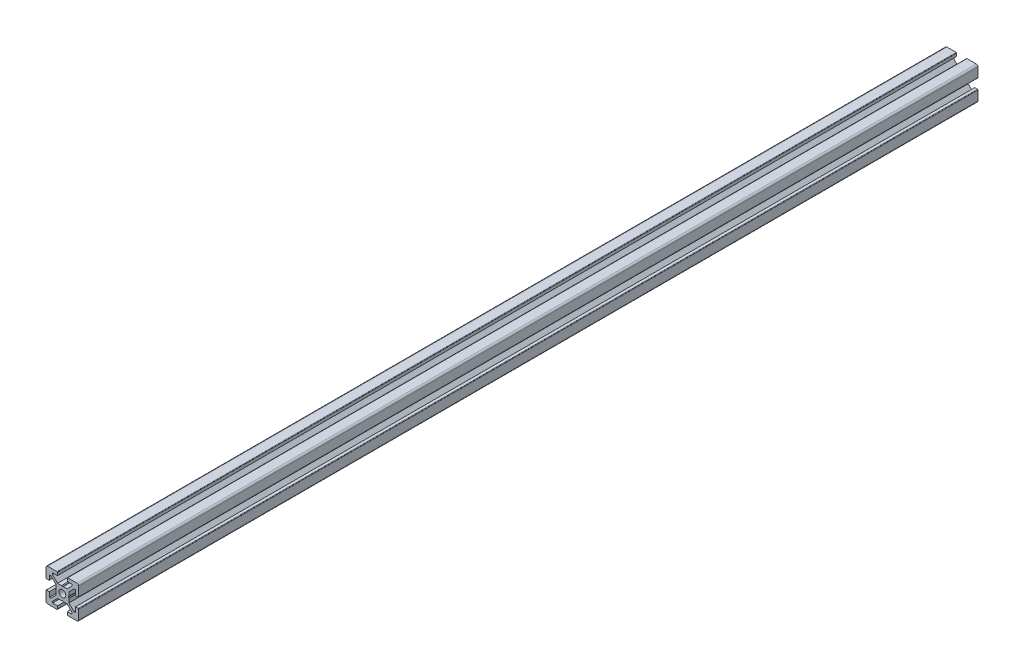
SolidWorks part; units mm, degrees
ref_plane "Front" through (0, 0, 0) normal (0, 0, 1) x (1, 0, 0)
ref_plane "Top" through (0, 0, 0) normal (0, 1, 0) x (1, 0, 0)
ref_plane "Right" through (0, 0, 0) normal (1, 0, 0) x (0, 0, -1)
ref_plane "Plane1" through (0, 0, 0) normal (0, 0, 1) x (1, 0, 0)
sketch "Sketch1" plane through (0, 0, 0) normal (0, 0, 1) x (1, 0, 0)
  line L0 (-10, 9) -> (-10, 3.3)
  line L1 (-9.7, 3) -> (-8, 3)
  line L2 (-8, 3) -> (-8, 6)
  line L3 (-8, 6) -> (-7.0607, 6)
  line L4 (-7.0607, 6) -> (-4, 2.9393)
  line L5 (-4, 2.9393) -> (-4, 0.5196)
  line L6 (-4, 0.5196) -> (-3.7, 0)
  line L7 (-3.7, 0) -> (-4, -0.5196)
  line L8 (-4, -0.5196) -> (-4, -2.9393)
  line L9 (-4, -2.9393) -> (-7.0607, -6)
  line L10 (-7.0607, -6) -> (-8, -6)
  line L11 (-8, -6) -> (-8, -3)
  line L12 (-8, -3) -> (-9.7, -3)
  line L13 (-10, -3.3) -> (-10, -9)
  line L14 (-9, -10) -> (-3.3, -10)
  line L15 (-3, -9.7) -> (-3, -8)
  line L16 (-3, -8) -> (-6, -8)
  line L17 (-6, -8) -> (-6, -7.0607)
  line L18 (-6, -7.0607) -> (-2.9393, -4)
  line L19 (-2.9393, -4) -> (-0.5196, -4)
  line L20 (-0.5196, -4) -> (0, -3.7)
  line L21 (0, -3.7) -> (0.5196, -4)
  line L22 (0.5196, -4) -> (2.9393, -4)
  line L23 (2.9393, -4) -> (6, -7.0607)
  line L24 (6, -7.0607) -> (6, -8)
  line L25 (6, -8) -> (3, -8)
  line L26 (3, -8) -> (3, -9.7)
  line L27 (3.3, -10) -> (9, -10)
  line L28 (10, -9) -> (10, -3.3)
  line L29 (9.7, -3) -> (8, -3)
  line L30 (8, -3) -> (8, -6)
  line L31 (8, -6) -> (7.0606, -6)
  line L32 (7.0606, -6) -> (4, -2.9393)
  line L33 (4, -2.9393) -> (4, -0.5196)
  line L34 (4, -0.5196) -> (3.7, 0)
  line L35 (3.7, 0) -> (4, 0.5196)
  line L36 (4, 0.5196) -> (4, 2.9393)
  line L37 (4, 2.9393) -> (7.0607, 6)
  line L38 (7.0607, 6) -> (8, 6)
  line L39 (8, 6) -> (8, 3)
  line L40 (8, 3) -> (9.7, 3)
  line L41 (10, 3.3) -> (10, 9)
  line L42 (9, 10) -> (3.3, 10)
  line L43 (3, 9.7) -> (3, 8)
  line L44 (3, 8) -> (6, 8)
  line L45 (6, 8) -> (6, 7.0607)
  line L46 (6, 7.0607) -> (2.9393, 4)
  line L47 (2.9393, 4) -> (0.5196, 4)
  line L48 (0.5196, 4) -> (0, 3.7)
  line L49 (0, 3.7) -> (-0.5196, 4)
  line L50 (-0.5196, 4) -> (-2.9394, 4)
  line L51 (-2.9394, 4) -> (-6, 7.0606)
  line L52 (-6, 7.0606) -> (-6, 8)
  line L53 (-6, 8) -> (-3, 8)
  line L54 (-3, 8) -> (-3, 9.7)
  line L55 (-3.3, 10) -> (-9, 10)
  arc A0 (-10, 3.3) -> (-9.7, 3) centre (-9.7, 3.3) ccw
  arc A1 (-9.7, -3) -> (-10, -3.3) centre (-9.7, -3.3) ccw
  arc A2 (-10, -9) -> (-9, -10) centre (-9, -9) ccw
  arc A3 (-3.3, -10) -> (-3, -9.7) centre (-3.3, -9.7) ccw
  arc A4 (3, -9.7) -> (3.3, -10) centre (3.3, -9.7) ccw
  arc A5 (9, -10) -> (10, -9) centre (9, -9) ccw
  arc A6 (10, -3.3) -> (9.7, -3) centre (9.7, -3.3) ccw
  arc A7 (9.7, 3) -> (10, 3.3) centre (9.7, 3.3) ccw
  arc A8 (10, 9) -> (9, 10) centre (9, 9) ccw
  arc A9 (3.3, 10) -> (3, 9.7) centre (3.3, 9.7) ccw
  arc A10 (-3, 9.7) -> (-3.3, 10) centre (-3.3, 9.7) ccw
  arc A11 (-9, 10) -> (-10, 9) centre (-9, 9) ccw
extrude "Boss-Extrude1" add sketch "Sketch1" against normal blind 550
ref_plane "Plane2" through (0, 0, 0) normal (1, 0, 0) x (0, 0, -1)
sketch "Sketch2" plane through (0, 0, 0) normal (1, 0, 0) x (0, 0, -1)
  line L0 (-0.8077, 0) -> (-0.8077, 2.1)
  line L1 (-0.8077, 2.1) -> (550, 2.1)
  line L2 (550, 2.1) -> (550, 0)
  line L3 (550, 0) -> (-0.8077, 0)
  line L4 (550, 0) -> (-0.8077, 0) construction
  line L5 (550, 0.5196) -> (550, 2.9393) construction
  point P4 (0, 0)
revolve "Cut-Revolve1" cut sketch "Sketch2" angle 360 about L4
